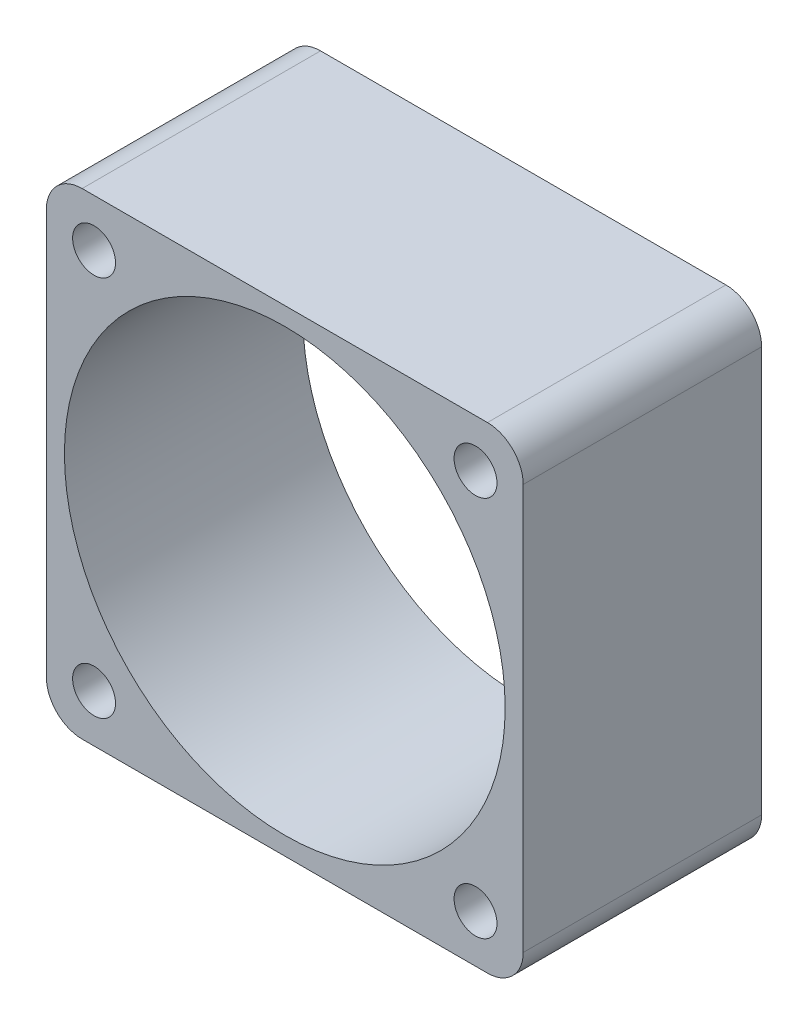
SolidWorks part; units mm, degrees
ref_plane "Front Plane" through (0, 0, 0) normal (0, 0, 1) x (1, 0, 0)
ref_plane "Top Plane" through (0, 0, 0) normal (0, 1, 0) x (1, 0, 0)
ref_plane "Right Plane" through (0, 0, 0) normal (1, 0, 0) x (0, 0, -1)
sketch "Sketch1" plane through (0, 0, 0) normal (0, 0, 1) x (1, 0, 0)
  line L1 (-20, -20) -> (20, -20)
  line L2 (-20, -20) -> (-20, 20)
  line L3 (-20, 20) -> (20, 20)
  line L4 (20, -20) -> (20, 20)
  line L5 (-20, -20) -> (20, 20) construction
  line L6 (-20, 20) -> (20, -20) construction
  line L7 (-16, 16) -> (16, 16) construction
  line L8 (-16, 16) -> (-16, -16) construction
  line L9 (-16, -16) -> (16, -16) construction
  line L10 (16, 16) -> (16, -16) construction
  line L11 (-16, 16) -> (16, -16) construction
  line L12 (-16, -16) -> (16, 16) construction
  circle A0 centre (-16, 16) radius 1.8
  circle A1 centre (16, 16) radius 1.8
  circle A2 centre (16, -16) radius 1.8
  circle A3 centre (-16, -16) radius 1.8
  circle A4 centre (0, 0) radius 18.4845
  point P0 (0, 0)
  point P6 (0, 0)
  point P21 (0, 0)
  dimension "D5" = 4
  dimension "D1" = 40
  dimension "D2" = 40
  dimension "D3" = 32
  dimension "D4" = 32
extrude "Boss-Extrude1" add sketch "Sketch1" along normal blind 20
fillet "Fillet1" radius 3 4 edges at (20, -20, 10) (-20, -20, 10) (-20, 20, 10) (20, 20, 10)
